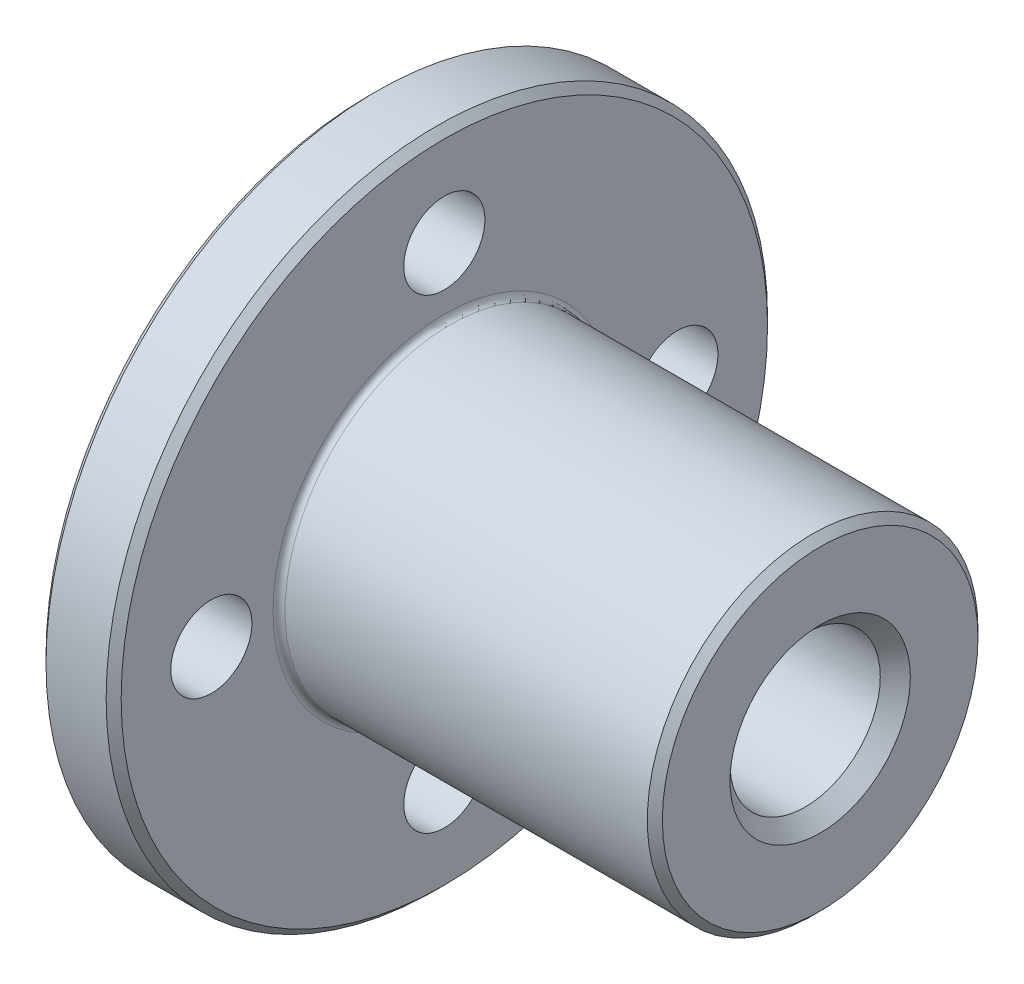
SolidWorks part; units mm, degrees
material "Ottone"
ref_plane "Piano frontale" through (0, 0, 0) normal (0, 0, 1) x (1, 0, 0)
ref_plane "Piano superiore" through (0, 0, 0) normal (0, 1, 0) x (1, 0, 0)
ref_plane "Piano destro" through (0, 0, 0) normal (1, 0, 0) x (0, 0, -1)
ref_plane "Plane1" through (0, 0, 0) normal (0, 0, -1) x (-1, 0, 0)
sketch "Sketch1" plane through (0, 0, 0) normal (0, 0, -1) x (-1, 0, 0)
  line L0 (-5, 22) -> (-5, 0)
  line L1 (-5, 0) -> (0, 0)
  line L2 (0, 0) -> (0, 22)
  line L3 (0, 22) -> (-5, 22)
  line L4 (-5, 0) -> (0, 0) construction
revolve "Revolve1" add sketch "Sketch1" angle 360 about L4
sketch "Sketch2" plane through (5, 0, 0) normal (1, 0, 0) x (0, 0, -1)
  circle A0 centre (0, 0) radius 11
extrude "Extrude1" add sketch "Sketch2" along normal blind 25
hole_wizard "HoleWzd1" positions "Sketch4" profile "Sketch3" hole size "Ø5.4" standard "Ansi Metric" end condition through all
sketch "Sketch4" plane through (5, 0, 0) normal (1, 0, 0) x (0, 0, -1)
  point P0 (0, -15.5)
  point P1 (15.5, 0)
  point P2 (-15.5, 0)
  point P3 (0, 15.5)
sketch "Sketch3" plane through (5, -15.5, 0) normal (0, 1, 0) x (0, 0, -1)
  line L0 (0, 0) -> (0, 5)
  line L1 (0, 5) -> (2.7, 5)
  line L2 (2.7, 5) -> (2.7, 0)
  line L5 (2.7, 0) -> (0, 0)
  line L11 (0, -6.35) -> (0, 107.95) construction
  dimension "Thru Hole Dia." = 5.4
  dimension "Thru Hole Depth" = 5
hole_wizard "HoleWzd2" positions "Sketch6" profile "Sketch5" hole size "Ø10.0" standard "Ansi Metric"
sketch "Sketch6" plane through (30, 0, 0) normal (1, 0, 0) x (0, 0, -1)
  point P0 (0, 0)
sketch "Sketch5" plane through (30, 0, 0) normal (0, 1, 0) x (0, 0, -1)
  line L0 (0, 0) -> (0, 30)
  line L1 (0, 30) -> (5, 30)
  line L2 (5, 30) -> (5, 0)
  line L5 (5, 0) -> (0, 0)
  line L11 (0, -6.35) -> (0, 107.95) construction
  dimension "Thru Hole Dia." = 10
  dimension "Thru Hole Depth" = 30
chamfer "Chamfer1" distance 0.5 angle 45 3 edges at (0, 0, 22) (30, 0, -11) (5, 0, 22)
chamfer "Chamfer2" distance 1 angle 45 2 edges at (0, 0, -5) (30, 0, -5)
fillet "Fillet1" radius 0.4 1 edges at (5, 0, -11)
